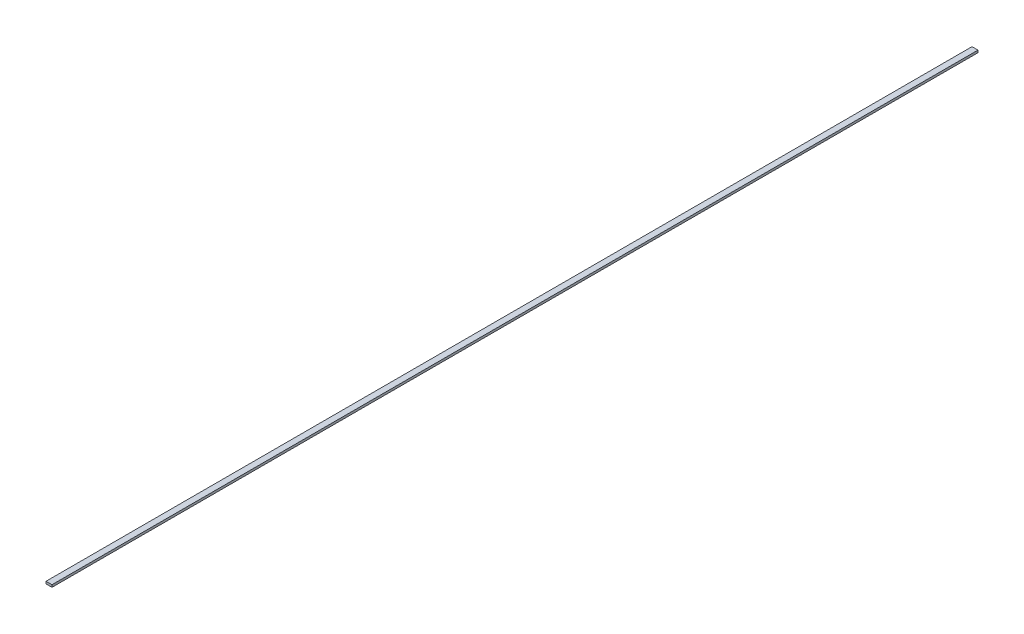
SolidWorks part; units mm, degrees
material "silicon D"
ref_plane "Front" through (0, 0, 0) normal (0, 0, 1) x (1, 0, 0)
ref_plane "Top" through (0, 0, 0) normal (0, 1, 0) x (1, 0, 0)
ref_plane "Right" through (0, 0, 0) normal (1, 0, 0) x (0, 0, -1)
sketch "Sketch1" plane through (0, 0, 0) normal (0, 1, 0) x (1, 0, 0)
  line L1 (-0.065, 10.0925) -> (0.065, 10.0925)
  line L2 (-0.065, 10.0925) -> (-0.065, -10.0925)
  line L3 (-0.065, -10.0925) -> (0.065, -10.0925)
  line L4 (0.065, 10.0925) -> (0.065, -10.0925)
  line L5 (-0.065, 10.0925) -> (0.065, 10.0075) construction
  line L6 (-0.065, 10.0925) -> (0.065, 10.0925) construction
  line L7 (-0.065, 10.0925) -> (-0.065, 10.0075) construction
  line L8 (-0.065, 10.0075) -> (0.065, 10.0075) construction
  line L9 (0.065, 10.0925) -> (0.065, 10.0075) construction
  line L10 (-0.065, -10.0075) -> (0.065, -10.0925) construction
  line L11 (-0.065, -10.0075) -> (0.065, -10.0075) construction
  line L12 (-0.065, -10.0075) -> (-0.065, -10.0925) construction
  line L13 (-0.065, -10.0925) -> (0.065, -10.0925) construction
  line L14 (0.065, -10.0075) -> (0.065, -10.0925) construction
  line L15 (0, 10.05) -> (0, -10.05) construction
  point P4 (0, 0)
  point P10 (0, 10.05)
  point P15 (0, -10.05)
  dimension "D3" = 0.13
  dimension "D4" = 0.085
  dimension "D5" = 20.1
extrude "Extrude1" add sketch "Sketch1" along normal blind 0.05
